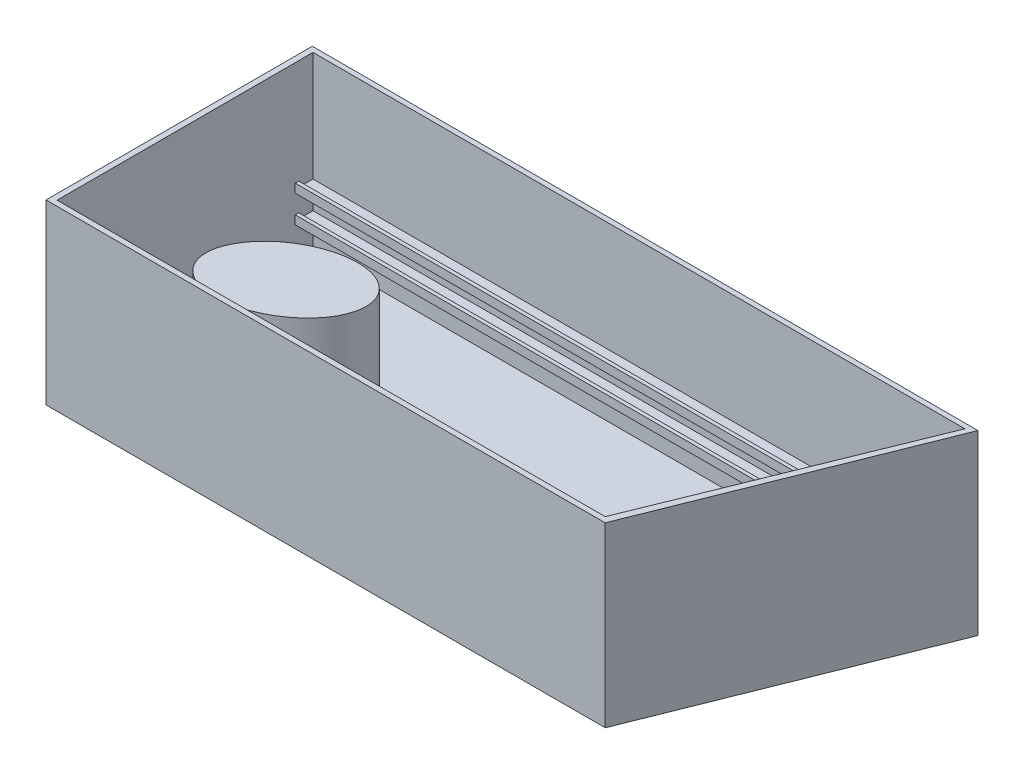
SolidWorks part; units mm, degrees
ref_plane "Front Plane" through (0, 0, 0) normal (0, 0, 1) x (1, 0, 0)
ref_plane "Top Plane" through (0, 0, 0) normal (0, 1, 0) x (1, 0, 0)
ref_plane "Right Plane" through (0, 0, 0) normal (1, 0, 0) x (0, 0, -1)
sketch "Sketch2" plane through (0, 0, 0) normal (0, 1, 0) x (1, 0, 0)
  line L0 (0, 0) -> (-8001, 0)
  line L1 (-8001, 0) -> (-8001, 3810)
  line L2 (-8001, 3810) -> (1524, 3810)
  line L3 (1524, 3810) -> (0, 0)
extrude "Boss-Extrude1" add sketch "Sketch2" along normal blind 2540
sketch "Sketch3" plane through (0, 2540, 0) normal (0, 1, 0) x (1, 0, 0)
  line L0 (-76.2, 76.2) -> (1408.6869, 3738.2428)
  line L1 (1408.6869, 3738.2428) -> (-7919.1199, 3738.2428)
  line L2 (-7919.1199, 3738.2428) -> (-7919.1199, 76.2)
  line L3 (-7919.1199, 76.2) -> (-76.2, 76.2)
  point P0 (-76.2, 76.2)
extrude "Cut-Extrude1" cut sketch "Sketch3" against normal blind 2463.8
sketch "Sketch4" plane through (0, 0, -3738.2428) normal (0, 0, 1) x (1, 0, 0)
  line L0 (-7919.1199, 76.2) -> (-7919.1199, 2540) construction
  line L1 (-7919.1199, 530.6421) -> (-7919.1199, 654.5386)
  line L2 (-7919.1199, 654.5386) -> (-730.518, 654.5386)
  line L3 (-730.518, 654.5386) -> (-730.518, 530.6421)
  line L4 (-730.518, 530.6421) -> (-7919.1199, 530.6421)
  point P0 (-7919.1199, 530.6421)
extrude "Boss-Extrude2" add sketch "Sketch4" along normal blind 254
sketch "Sketch5" plane through (0, 0, -3738.2428) normal (0, 0, 1) x (1, 0, 0)
  line L0 (-7919.1199, 654.5386) -> (-7919.1199, 2540) construction
  line L1 (-7919.1199, 922.7203) -> (-7919.1199, 1047.1803)
  line L2 (-7919.1199, 1047.1803) -> (-730.5389, 1047.1803)
  line L3 (-7919.1199, 922.7203) -> (-730.5389, 922.7203)
  line L4 (-730.5389, 922.7203) -> (-730.5389, 1047.1803)
  point P0 (-7919.1199, 922.7203)
extrude "Boss-Extrude3" add sketch "Sketch5" along normal blind 254 contours L4 L2 L1 L3
sketch "Sketch6" plane through (0, 1047.1803, 0) normal (0, 1, 0) x (1, 0, 0)
  line L0 (-7919.1199, 3738.2428) -> (-7919.1199, 3535.0428)
  line L1 (-7919.1199, 3484.2428) -> (-7919.1199, 3738.2428) construction
  line L2 (-7919.1199, 3535.0428) -> (-730.5389, 3535.0428)
  line L3 (-730.5389, 3484.2428) -> (-730.5389, 3738.2428) construction
  line L4 (-730.5389, 3535.0428) -> (-730.5389, 3738.2428)
  line L5 (-730.5389, 3738.2428) -> (-7919.1199, 3738.2428)
extrude "Cut-Extrude2" cut sketch "Sketch6" against normal blind 76.2
sketch "Sketch11" plane through (0, 654.5386, 0) normal (0, 1, 0) x (1, 0, 0)
  line L0 (-7919.1199, 3738.2428) -> (-7919.1199, 3535.0428)
  line L1 (-7919.1199, 3484.2428) -> (-7919.1199, 3738.2428) construction
  line L2 (-7919.1199, 3535.0428) -> (-730.518, 3535.0428)
  line L3 (-730.518, 3484.2428) -> (-730.518, 3738.2428) construction
  line L4 (-730.518, 3535.0428) -> (-730.518, 3738.2428)
  line L5 (-730.518, 3738.2428) -> (-7919.1199, 3738.2428)
extrude "Cut-Extrude3" cut sketch "Sketch11" against normal blind 76.2
sketch "Sketch18" plane through (0, 76.2, 0) normal (0, 1, 0) x (1, 0, 0)
  ellipse E0 centre (-5727.9513, 1161.6662) end of major axis (-4873.4676, 1614.2103) minor radius 638.6246
extrude "Boss-Extrude4" add sketch "Sketch18" along normal blind 2032 contours E0
